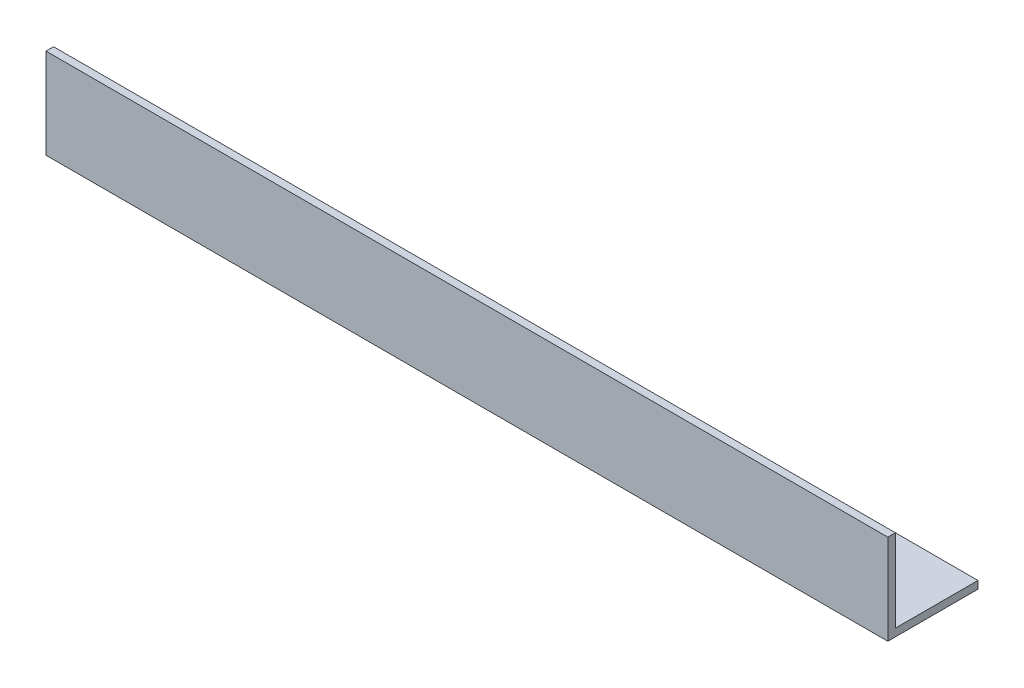
SolidWorks part; units mm, degrees
material "6061-T6 (SS)"
ref_plane "Front Plane" through (0, 0, 0) normal (0, 0, 1) x (1, 0, 0)
ref_plane "Top Plane" through (0, 0, 0) normal (0, 1, 0) x (1, 0, 0)
ref_plane "Right Plane" through (0, 0, 0) normal (1, 0, 0) x (0, 0, -1)
sketch "Sketch1" plane through (0, 0, 0) normal (1, 0, 0) x (0, 0, -1)
  line L0 (0, 0) -> (0, 19.05)
  line L1 (0, 19.05) -> (1.6002, 19.05)
  line L2 (1.6002, 19.05) -> (1.6002, 1.6002)
  line L3 (1.6002, 1.6002) -> (19.05, 1.6002)
  line L4 (19.05, 1.6002) -> (19.05, 0)
  line L5 (19.05, 0) -> (0, 0)
  dimension "D1" = 19.05
  dimension "D2" = 1.6002
extrude "Boss-Extrude1" add sketch "Sketch1" along normal blind 177.8
